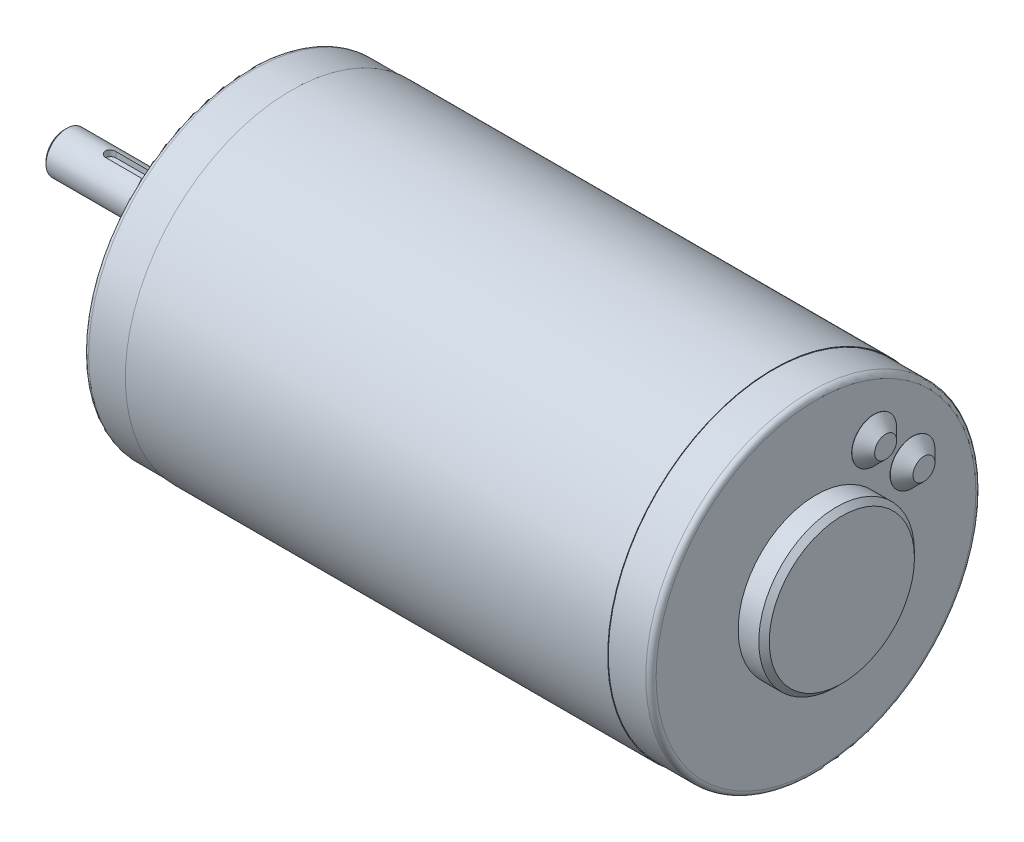
SolidWorks part; units mm, degrees
ref_plane "Front Plane" through (0, 0, 0) normal (0, 0, 1) x (1, 0, 0)
ref_plane "Top Plane" through (0, 0, 0) normal (0, 1, 0) x (1, 0, 0)
ref_plane "Right Plane" through (0, 0, 0) normal (1, 0, 0) x (0, 0, -1)
sketch "Sketch1" plane through (0, 0, 0) normal (0, 0, 1) x (1, 0, 0)
  line L0 (8.2296, 32.004) -> (8.2296, 0)
  line L1 (8.2296, 0) -> (101.3704, 0)
  line L2 (101.3704, 0) -> (101.3704, 32.004)
  line L3 (101.3704, 32.004) -> (8.2296, 32.004)
  line L4 (8.2296, 0) -> (101.3704, 0) construction
revolve "Revolve1" add sketch "Sketch1" angle 360 about L4
sketch "Sketch2" plane through (101.3704, 0, 0) normal (1, 0, 0) x (0, 0, -1)
  circle A0 centre (0, 0) radius 31.877
extrude "Boss-Extrude1" add sketch "Sketch2" along normal blind 8.2296
sketch "Sketch3" plane through (109.6, 0, 0) normal (1, 0, 0) x (0, 0, -1)
  circle A0 centre (0, 0) radius 15.0368
extrude "Boss-Extrude2" add sketch "Sketch3" along normal blind 3.984
sketch "Sketch4" plane through (113.584, 0, 0) normal (1, 0, 0) x (0, 0, -1)
  circle A0 centre (0, 0) radius 15.0368
extrude "Boss-Extrude3" add sketch "Sketch4" along normal blind 1.016 draft 45
sketch "Sketch5" plane through (8.2296, 0, 0) normal (-1, 0, 0) x (0, 0, 1)
  circle A0 centre (0, 0) radius 31.877
extrude "Boss-Extrude4" add sketch "Sketch5" along normal blind 8.2296
sketch "Sketch6" plane through (0, 0, 0) normal (-1, 0, 0) x (0, 0, 1)
  circle A0 centre (0, 0) radius 9.525
extrude "Boss-Extrude5" add sketch "Sketch6" along normal blind 4
sketch "Sketch7" plane through (-4, 0, 0) normal (-1, 0, 0) x (0, 0, 1)
  circle A0 centre (0, 0) radius 4
extrude "Boss-Extrude6" add sketch "Sketch7" along normal blind 31.6
imported_body "Surface-Imported1"
ref_plane "Plane1" through (0, 2.8, 0) normal (0, -1, 0) x (1, 0, 0)
sketch "Sketch8" plane through (0, 2.8, 0) normal (0, -1, 0) x (1, 0, 0)
  line L0 (-7.1, 1) -> (-26.6, 1)
  line L1 (-26.6, -1) -> (-7.1, -1)
  arc A0 (-7.1, -1) -> (-7.1, 1) centre (-7.1, 0) ccw
  arc A1 (-26.6, 1) -> (-26.6, -1) centre (-26.6, 0) ccw
extrude "Cut-Extrude1" cut sketch "Sketch8" against normal up to surface
ref_plane "Plane2" through (0, 0, -18.6071) normal (0, 0, 1) x (1, 0, 0)
sketch "Sketch9" plane through (0, 0, -18.6071) normal (0, 0, 1) x (1, 0, 0)
  line L0 (109.6, 15.5254) -> (109.6, 11.2074)
  line L1 (109.6, 11.2074) -> (111.8479, 11.2074)
  line L2 (111.8479, 11.2074) -> (111.8479, 13.3254)
  line L3 (111.8479, 13.3254) -> (109.6479, 15.5254)
  line L4 (109.6479, 15.5254) -> (109.6, 15.5254)
  line L5 (109.6, 11.2074) -> (111.8479, 11.2074) construction
revolve "Revolve2" add sketch "Sketch9" angle 360 about L5
ref_plane "Plane3" through (0, 0, -11.2074) normal (0, 0, 1) x (1, 0, 0)
sketch "Sketch10" plane through (0, 0, -11.2074) normal (0, 0, 1) x (1, 0, 0)
  line L0 (109.6, 22.9251) -> (109.6, 18.6071)
  line L1 (109.6, 18.6071) -> (111.8479, 18.6071)
  line L2 (111.8479, 18.6071) -> (111.8479, 20.7251)
  line L3 (111.8479, 20.7251) -> (109.6479, 22.9251)
  line L4 (109.6479, 22.9251) -> (109.6, 22.9251)
  line L5 (109.6, 18.6071) -> (111.8479, 18.6071) construction
revolve "Revolve3" add sketch "Sketch10" angle 360 about L5
hole_wizard "#21 (0.159) Diameter Hole1" positions "Sketch12" profile "Sketch11" hole size "#21" standard "ANSI Inch"
sketch "Sketch12" plane through (0, 0, 0) normal (-1, 0, 0) x (0, 0, 1)
  point P0 (0, 25.4)
  point P1 (0, -25.4)
sketch "Sketch11" plane through (0, 25.4, 0) normal (0, 1, 0) x (0, 0, 1)
  line L0 (0, 0) -> (0, 14.8277)
  line L1 (0, 14.8277) -> (2.0193, 13.6144)
  line L2 (2.0193, 13.6144) -> (2.0193, 0)
  line L5 (2.0193, 0) -> (0, 0)
  line L10 (0, 14.8277) -> (-2.0193, 13.6144) construction
  line L11 (0, -6.35) -> (0, 107.95) construction
  dimension "Hole Dia." = 4.0386
  dimension "Hole Depth" = 13.6144
  dimension "Drill Angle" = 118
chamfer "Chamfer1" distance 1.016 angle 45 1 edges at (-4, 0, 9.525)
chamfer "Chamfer2" distance 0.5 angle 45 1 edges at (-35.6, 0, 4)
fillet "Fillet1" radius 1 2 edges at (109.6, 0, -31.877) (0, 0, 31.877)
